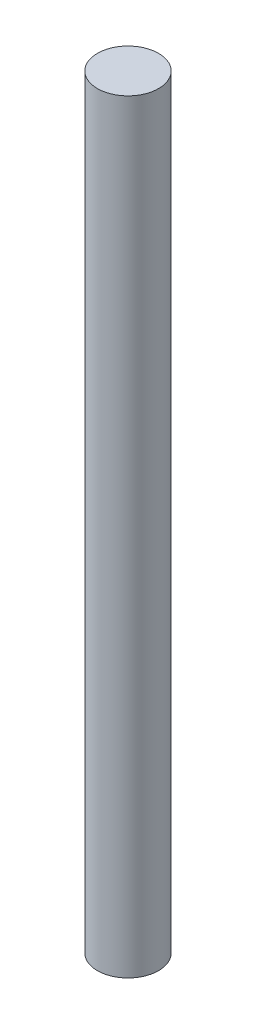
SolidWorks part; units mm, degrees
material "1.5714 (16NiCr4)"
ref_plane "Plan de face" through (0, 0, 0) normal (0, 0, 1) x (1, 0, 0)
ref_plane "Plan de dessus" through (0, 0, 0) normal (0, 1, 0) x (1, 0, 0)
ref_plane "Plan de droite" through (0, 0, 0) normal (1, 0, 0) x (0, 0, -1)
sketch "Esquisse1" plane through (0, 0, 0) normal (0, 1, 0) x (1, 0, 0)
  circle A0 centre (0, 0) radius 3
  dimension "D1" = 6
extrude "Boss.-Extru.1" add sketch "Esquisse1" along normal blind 75
